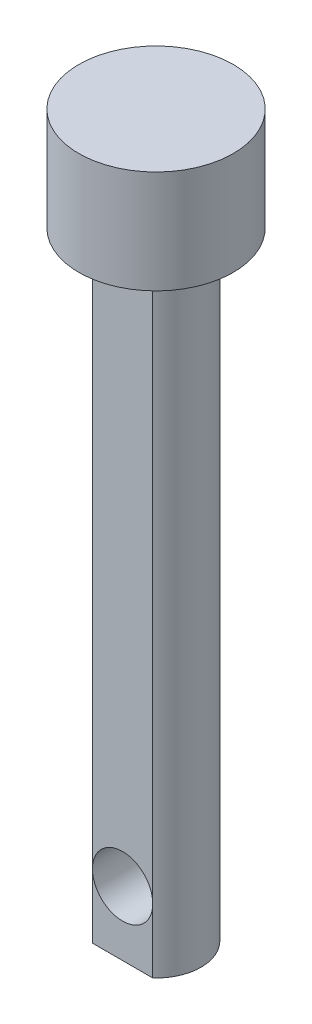
SolidWorks part; units mm, degrees
ref_plane "Front Plane" through (0, 0, 0) normal (0, 0, 1) x (1, 0, 0)
ref_plane "Top Plane" through (0, 0, 0) normal (0, 1, 0) x (1, 0, 0)
ref_plane "Right Plane" through (0, 0, 0) normal (1, 0, 0) x (0, 0, -1)
sketch "Sketch2" plane through (0, 0, 0) normal (1, 0, 0) x (0, 0, -1)
  line L13 (0, 0) -> (0, 28)
  line L14 (0, 28) -> (-3, 28)
  line L15 (-3, 28) -> (-3, 24)
  line L16 (-3, 24) -> (-1.75, 24)
  line L17 (-1.75, 24) -> (-1.75, 0)
  line L18 (-1.75, 0) -> (0, 0)
  dimension "D1" = 4
  dimension "D2" = 3
  dimension "D3" = 28
  dimension "D4" = 1.75
revolve "Revolve1" add sketch "Sketch2" angle 360 about L13
sketch "Sketch3" plane through (0, 0, 0) normal (0, -1, 0) x (1, 0, 0)
  line L0 (-1.1715, 1.3) -> (1.1715, 1.3)
  line L1 (-2.4367, -1.75) -> (2.4367, -1.75) construction
  circle A0 centre (0, 0) radius 1.75 construction
  circle A1 centre (0, 0) radius 1.75
  arc A2 (1.1715, 1.3) -> (-1.1715, 1.3) centre (0, 0) ccw
  circle A3 centre (0, 0) radius 3 construction
  dimension "D2" = 3.05
  dimension "D1" = 0
extrude "Cut-Extrude1" cut sketch "Sketch3" against normal up to surface (24 mm away) up to face at (0, 24, -1.75)
sketch "Sketch4" plane through (0, 0, 1.3) normal (0, 0, 1) x (1, 0, 0)
  line L0 (-1.1715, 24) -> (-1.1715, 0) construction
  line L1 (1.1715, 24) -> (1.1715, 0) construction
  line L2 (-1.1715, 0) -> (1.1715, 0) construction
  circle A0 centre (0, 2.5) radius 1.1715
  dimension "D1" = 2.5
extrude "Cut-Extrude2" cut sketch "Sketch4" against normal through all
